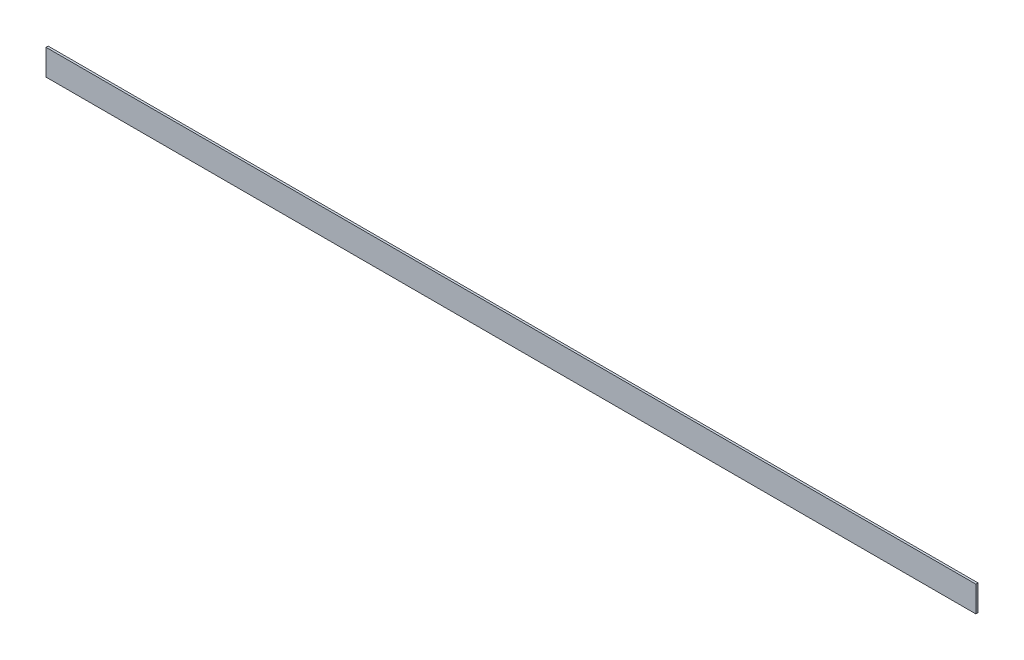
SolidWorks part; units mm, degrees
material "PVC 0.007 Plasticized"
ref_plane "Front Plane" through (0, 0, 0) normal (0, 0, 1) x (1, 0, 0)
ref_plane "Top Plane" through (0, 0, 0) normal (0, 1, 0) x (1, 0, 0)
ref_plane "Right Plane" through (0, 0, 0) normal (1, 0, 0) x (0, 0, -1)
sketch "Sketch1" plane through (0, 0, 0) normal (1, 0, 0) x (0, 0, -1)
  line L1 (-3.175, -38.1) -> (3.175, -38.1)
  line L2 (-3.175, -38.1) -> (-3.175, 38.1)
  line L3 (-3.175, 38.1) -> (3.175, 38.1)
  line L4 (3.175, -38.1) -> (3.175, 38.1)
  line L5 (-3.175, -38.1) -> (3.175, 38.1) construction
  line L6 (-3.175, 38.1) -> (3.175, -38.1) construction
  point P0 (0, 0)
  dimension "D1" = 76.2
  dimension "D2" = 6.35
extrude "Boss-Extrude1" add sketch "Sketch1" along normal blind 2743.2
equation "\"D2@Sketch1\"=1in/4"
